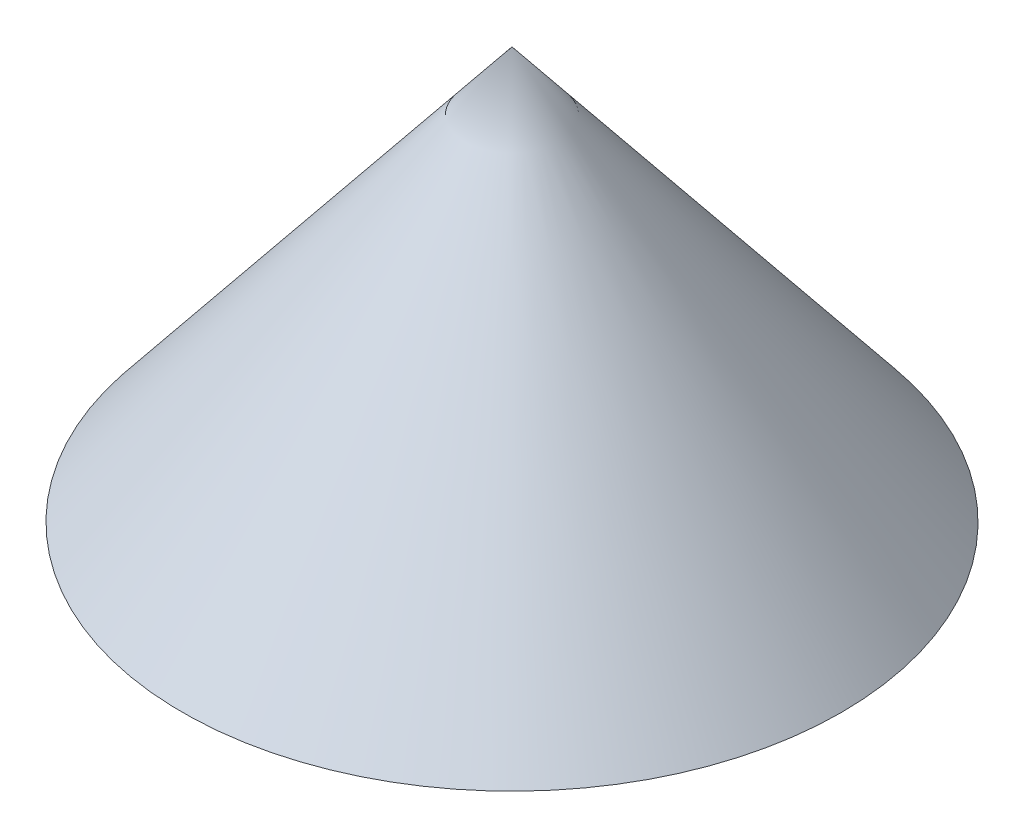
SolidWorks part; units mm, degrees
ref_plane "Front Plane" through (0, 0, 0) normal (0, 0, 1) x (1, 0, 0)
ref_plane "Top Plane" through (0, 0, 0) normal (0, 1, 0) x (1, 0, 0)
ref_plane "Right Plane" through (0, 0, 0) normal (1, 0, 0) x (0, 0, -1)
sketch "Sketch1" plane through (0, 0, 0) normal (0, 0, 1) x (1, 0, 0)
  line L0 (0, 0) -> (0, 62.45) construction
  line L1 (0, 0) -> (25, 0)
  line L2 (25, 0) -> (0, 31.225)
  line L3 (0, 31.225) -> (0, 0)
  dimension "D1" = 25
  dimension "D2" = 40
revolve "Revolve1" add sketch "Sketch1" angle 360 about L0
